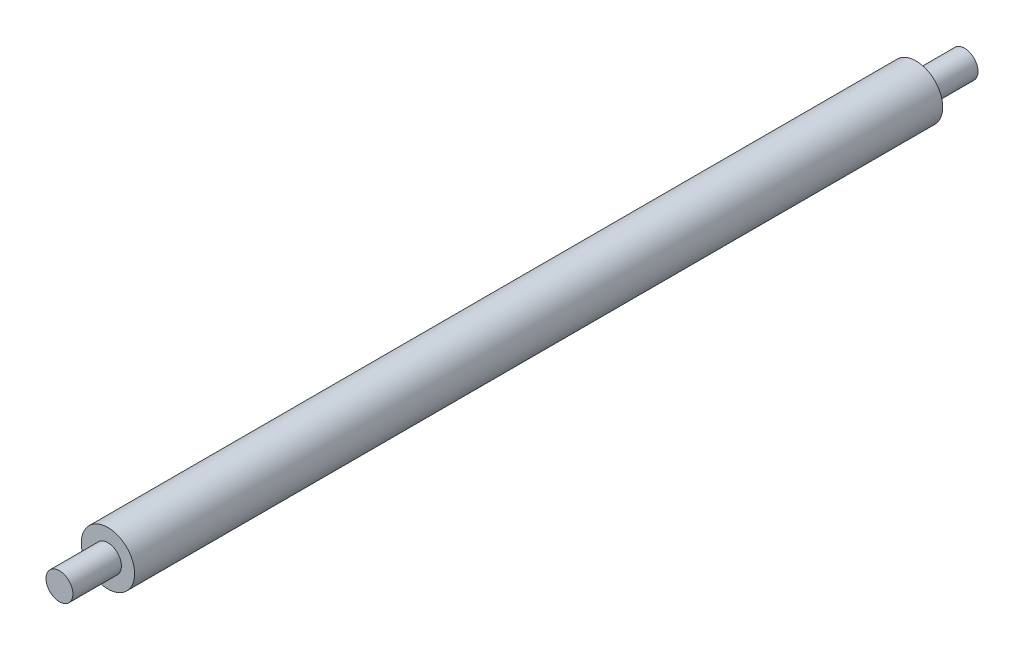
SolidWorks part; units mm, degrees
ref_plane "Front Plane" through (0, 0, 0) normal (0, 0, 1) x (1, 0, 0)
ref_plane "Top Plane" through (0, 0, 0) normal (0, 1, 0) x (1, 0, 0)
ref_plane "Right Plane" through (0, 0, 0) normal (1, 0, 0) x (0, 0, -1)
sketch "Sketch1" plane through (0, 0, 0) normal (0, 0, 1) x (1, 0, 0)
  circle A1 centre (0, 0) radius 21.75
  circle A2 centre (0, 0) radius 24.75
extrude "Boss-Extrude1" add sketch "Sketch1" along normal blind 750
sketch "Sketch2" plane through (0, 0, 0) normal (0, 0, 1) x (1, 0, 0)
  circle A0 centre (0, 0) radius 21.75
  circle A1 centre (0, 0) radius 12.5
extrude "Boss-Extrude2" add sketch "Sketch2" along normal blind 5
sketch "Sketch3" plane through (0, 0, 750) normal (0, 0, 1) x (1, 0, 0)
  circle A0 centre (0, 0) radius 21.75
  circle A1 centre (0, 0) radius 12.5
extrude "Boss-Extrude3" add sketch "Sketch3" against normal blind 5
sketch "Sketch4" plane through (0, 0, 750) normal (0, 0, 1) x (1, 0, 0)
  circle A0 centre (0, 0) radius 12.5
extrude "Boss-Extrude4" add sketch "Sketch4" along normal blind 45 and the other way blind 5
sketch "Sketch5" plane through (0, 0, 0) normal (0, 0, -1) x (-1, 0, 0)
  circle A0 centre (0, 0) radius 12.5
extrude "Boss-Extrude5" add sketch "Sketch5" along normal blind 45 and the other way blind 5
